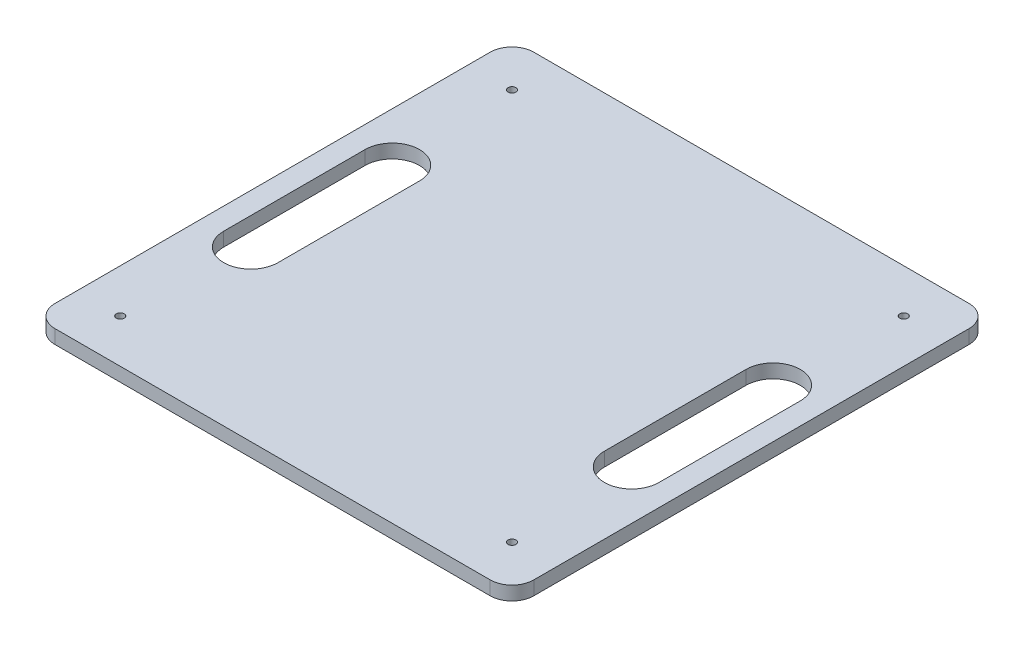
SolidWorks part; units mm, degrees
material "Acrylic (Medium-high impact)"
ref_plane "Front Plane" through (0, 0, 0) normal (0, 0, 1) x (1, 0, 0)
ref_plane "Top Plane" through (0, 0, 0) normal (0, 1, 0) x (1, 0, 0)
ref_plane "Right Plane" through (0, 0, 0) normal (1, 0, 0) x (0, 0, -1)
sketch "Sketch2" plane through (0, 0, 0) normal (0, 1, 0) x (1, 0, 0)
  line L1 (-110, 110) -> (110, 110)
  line L2 (-110, 110) -> (-110, -110)
  line L3 (-110, -110) -> (110, -110)
  line L4 (110, 110) -> (110, -110)
  line L5 (-110, 110) -> (110, -110) construction
  line L6 (-110, -110) -> (110, 110) construction
  point P0 (0, 0)
extrude "Boss-Extrude1" add sketch "Sketch2" along normal blind 6.35
sketch "Sketch3" plane through (0, 0, 0) normal (0, -1, 0) x (-1, 0, 0)
  line L0 (90, -100) -> (-90, -100) construction
  line L1 (-100, -90) -> (-100, 90) construction
  circle A0 centre (90, -90) radius 1.8
  circle A2 centre (90, 90) radius 1.8
  circle A3 centre (-90, 90) radius 1.8
  circle A4 centre (-90, -90) radius 1.8
  dimension "D1" = 10
  dimension "D2" = 10
extrude "Cut-Extrude1" cut sketch "Sketch3" against normal blind 6.35
fillet "Fillet1" radius 10 4 edges at (110, 3.175, -110) (-110, 3.175, -110) (-110, 3.175, 110) (110, 3.175, 110)
sketch "Sketch7" plane through (0, 6.35, 0) normal (0, 1, 0) x (1, 0, 0)
  line L0 (-87.5, 45) -> (-87.5, 29.7788) construction
  line L2 (-100, 32.5) -> (-100, -32.5)
  line L4 (-75, 32.5) -> (-75, -32.5)
  line L5 (100, 110) -> (-100, 110) construction
  line L6 (0, 110) -> (0, -115.7737) construction
  line L7 (-110, 100) -> (-110, -100) construction
  line L8 (75, 32.5) -> (75, -32.5)
  line L9 (100, 32.5) -> (100, -32.5)
  arc A0 (-75, 32.5) -> (-100, 32.5) centre (-87.5, 32.5) ccw
  arc A1 (-100, -32.5) -> (-75, -32.5) centre (-87.5, -32.5) ccw
  arc A2 (100, -32.5) -> (75, -32.5) centre (87.5, -32.5) cw
  arc A3 (75, 32.5) -> (100, 32.5) centre (87.5, 32.5) cw
  point P3 (-100, 0)
  point P11 (-87.5, -45)
  dimension "D2" = 12.5
  dimension "D1" = 110
  dimension "D3" = 90
  dimension "D4" = 10
extrude "Cut-Extrude2" cut sketch "Sketch7" against normal blind 10
